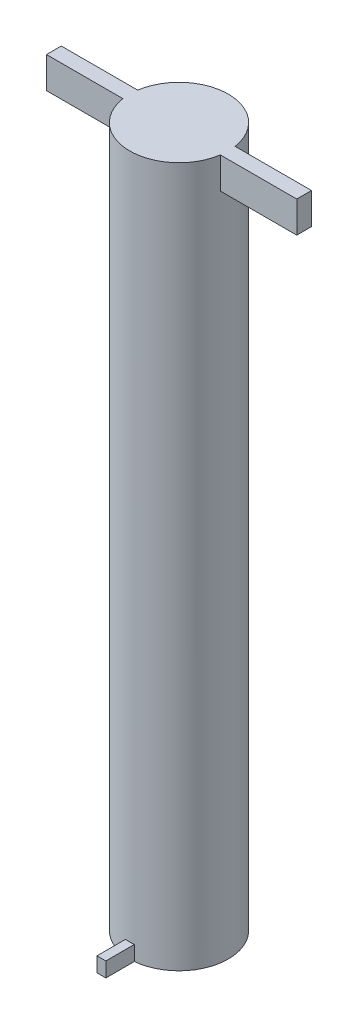
SolidWorks part; units mm, degrees
ref_plane "Front Plane" through (0, 0, 0) normal (0, 0, 1) x (1, 0, 0)
ref_plane "Top Plane" through (0, 0, 0) normal (0, 1, 0) x (1, 0, 0)
ref_plane "Right Plane" through (0, 0, 0) normal (1, 0, 0) x (0, 0, -1)
sketch "Sketch1" plane through (0, 0, 0) normal (0, 1, 0) x (1, 0, 0)
  circle A0 centre (0, 0) radius 10
  dimension "D1" = 20
extrude "Boss-Extrude1" add sketch "Sketch1" along normal blind 142.05
sketch "Sketch3" plane through (0, 0, 0) normal (0, -1, 0) x (1, 0, 0)
  line L1 (-0.9, 15.75) -> (0.9, 15.75)
  line L2 (-0.9, 15.75) -> (-0.9, 9.3548)
  line L4 (0.9, 15.75) -> (0.9, 9.3548)
  arc A0 (0.9, 9.3548) -> (-0.9, 9.3548) centre (0, 0) ccw
  dimension "D1" = 0.9
  dimension "D3" = 15.75
extrude "Boss-Extrude2" add sketch "Sketch3" against normal blind 3
sketch "Sketch4" plane through (0, 142.05, 0) normal (0, 1, 0) x (1, 0, 0)
  line L1 (-25.4, 1.5) -> (25.4, 1.5)
  line L2 (-25.4, 1.5) -> (-25.4, -1.5)
  line L3 (-25.4, -1.5) -> (25.4, -1.5)
  line L4 (25.4, 1.5) -> (25.4, -1.5)
  point P4 (-25.4, 0)
  point P5 (0, 1.5)
  dimension "D1" = 50.8
  dimension "D2" = 3
extrude "Boss-Extrude3" add sketch "Sketch4" against normal blind 6.35
sketch "Sketch5" plane through (0, 0, 0) normal (0, -1, 0) x (1, 0, 0)
  circle A0 centre (0, 0) radius 6
  dimension "D1" = 12
extrude "Cut-Extrude1" cut sketch "Sketch5" against normal blind 3
